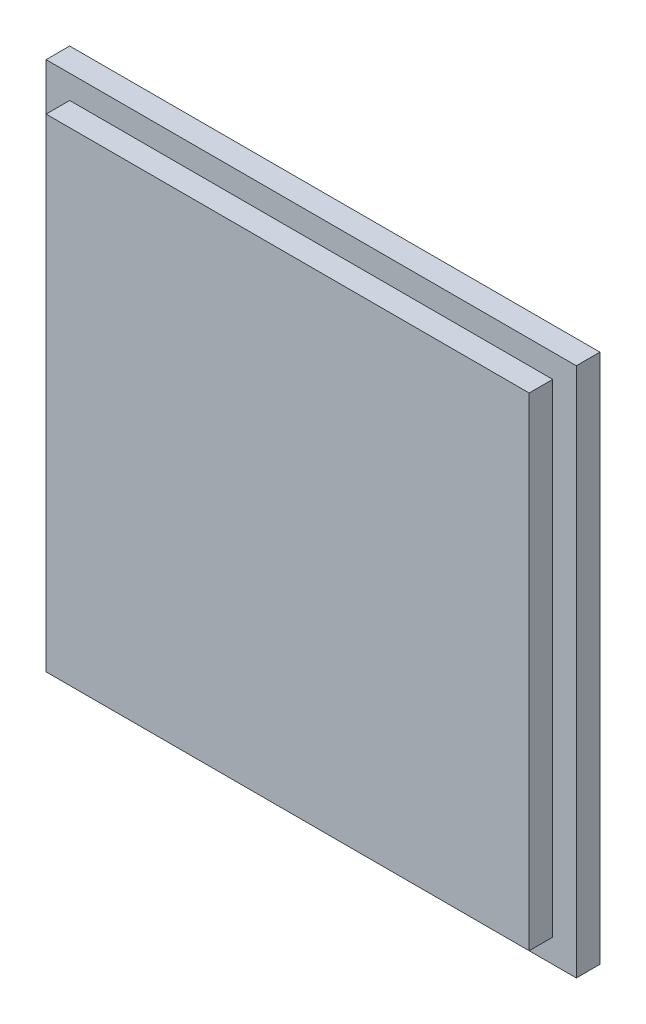
SolidWorks part; units mm, degrees
ref_plane "Front Plane" through (0, 0, 0) normal (0, 0, 1) x (1, 0, 0)
ref_plane "Top Plane" through (0, 0, 0) normal (0, 1, 0) x (1, 0, 0)
ref_plane "Right Plane" through (0, 0, 0) normal (1, 0, 0) x (0, 0, -1)
sketch "Sketch2" plane through (0, 0, 0) normal (0, 0, 1) x (1, 0, 0)
  line L1 (-28.1, -28.1) -> (28.1, -28.1)
  line L2 (-28.1, -28.1) -> (-28.1, 28.1)
  line L3 (-28.1, 28.1) -> (28.1, 28.1)
  line L4 (28.1, -28.1) -> (28.1, 28.1)
  line L5 (-28.1, -28.1) -> (28.1, 28.1) construction
  line L6 (-28.1, 28.1) -> (28.1, -28.1) construction
  point P0 (0, 0)
extrude "Boss-Extrude1" add sketch "Sketch2" along normal blind 2.5
sketch "Sketch3" plane through (0, 0, 2.5) normal (0, 0, 1) x (1, 0, 0)
  line L1 (-25.6, -25.6) -> (25.6, -25.6)
  line L2 (-25.6, -25.6) -> (-25.6, 25.6)
  line L3 (-25.6, 25.6) -> (25.6, 25.6)
  line L4 (25.6, -25.6) -> (25.6, 25.6)
  line L5 (-25.6, -25.6) -> (25.6, 25.6) construction
  line L6 (-25.6, 25.6) -> (25.6, -25.6) construction
  point P0 (0, 0)
extrude "Boss-Extrude2" add sketch "Sketch3" along normal blind 2.5
sketch "Sketch4" plane through (0, 0, 0) normal (0, 0, -1) x (-1, 0, 0)
  line L3 (0, 20) -> (-17.3205, -10)
  line L4 (17.3205, -10) -> (-17.3205, -10)
  line L5 (17.3205, -10) -> (0, 20)
extrude "Cut-Extrude1" cut sketch "Sketch4" against normal blind 1
sketch "Sketch5" plane through (0, 0, 1) normal (0, 0, -1) x (-1, 0, 0)
  line L0 (-1.5178, 12.4615) -> (-5.5616, 1.6429)
  line L1 (-5.5616, 1.6429) -> (-0.5744, 2.168)
  line L2 (-0.5744, 2.168) -> (-2.8832, -4.9218)
  line L3 (-2.8832, -4.9218) -> (-4.1962, -3.6614)
  line L4 (-4.1962, -3.6614) -> (-3.3034, -8.388)
  line L5 (-3.3034, -8.388) -> (0.3204, -5.447)
  line L6 (0.3204, -5.447) -> (-1.5178, -5.447)
  line L7 (-1.5178, -5.447) -> (2.6311, 5.109)
  line L8 (2.6311, 5.109) -> (-1.4652, 4.9515)
  line L9 (-1.4652, 4.9515) -> (2.3685, 12.3565)
  line L10 (2.3685, 12.3565) -> (-1.5178, 12.4615)
  point P11 (0, 1.6771)
  point P12 (-4.9873, 1.1519)
  point P13 (0.5829, 5.0303)
extrude "Boss-Extrude3" add sketch "Sketch5" along normal blind 1
